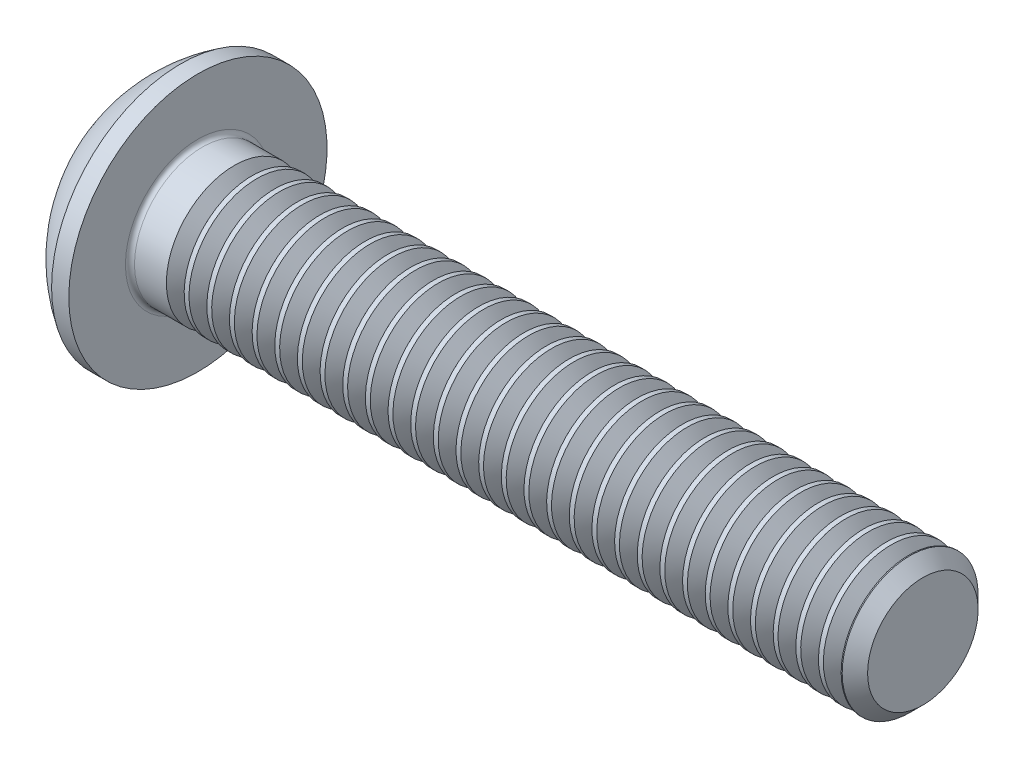
SolidWorks part; units mm, degrees
ref_plane "Plane1" through (0, 0, 0) normal (0, 0, 1) x (1, 0, 0)
ref_plane "Plane2" through (0, 0, 0) normal (0, 1, 0) x (1, 0, 0)
ref_plane "Plane3" through (0, 0, 0) normal (1, 0, 0) x (0, 0, -1)
sketch "BodySke" plane through (0, 0, 0) normal (0, 0, 1) x (1, 0, 0)
  line L0 (17.65, 0) -> (17.65, 1.2195)
  line L1 (17.3695, 1.5) -> (1.65, 1.5)
  line L2 (1.65, 1.5) -> (1.65, 2.85)
  line L3 (1.65, 2.85) -> (1.27, 2.85)
  line L4 (0, 0) -> (101.6, 0) construction
  line L5 (1.65, -2.85) -> (1.27, -2.85) construction
  line L6 (55.6768, -1.5) -> (1.65, -1.5) construction
  line L7 (17.65, 0) -> (0, 0)
  line L8 (0, 1.425) -> (0, -1.425) construction
  line L9 (0, 0) -> (0, 1.425)
  line L10 (17.65, 1.2195) -> (17.3695, 1.5)
  line L11 (17.65, -1.2195) -> (17.3695, -1.5) construction
  line L12 (2.15, 9.525) -> (2.15, -1.5) construction
  line L13 (1.65, 9.525) -> (1.65, -1.5) construction
  arc A1 (0, 1.425) -> (1.27, 2.85) centre (3.0334, 0) cw
  dimension "Diameter" = 3
  dimension "Length" = 16
  dimension "Head_dia" = 5.7
  dimension "D1" = 2.85
  dimension "Head_ht" = 1.65
  dimension "Head_side_ht" = 0.38
  dimension "Minor_dia" = 2.439
  dimension "Body_ch_ang" = 45
  dimension "Advance" = 0.5
  dimension "Thread_nom" = 16
revolve "BaseBody" add sketch "BodySke" angle 360 about L4
cosmetic thread "ThreadCosmetic" [suppressed] parameters "Thread_length"=15, "Thread_minor"=2.439
fillet "Fillet1" radius 0.1 1 edges at (1.65, 0, 1.5)
sketch "Sketch2" plane through (0, 0, 0) normal (0, 0, 1) x (1, 0, 0)
  line L0 (0, 1) -> (1.04, 1)
  line L1 (1.04, 1) -> (1.6174, 0)
  line L3 (1.6174, 0) -> (0, 0)
  line L4 (0, 0) -> (0, 1)
  line L5 (0, -1) -> (1.04, -1) construction
  line L6 (0, 0) -> (47.625, 0) construction
  dimension "D2" = 60
  dimension "PreBroach_depth" = 1.04
  dimension "PreBroach_dia" = 2
revolve "PreBroach" cut sketch "Sketch2" angle 360 about L6
sketch "Sketch3" plane through (0, 0, 0) normal (1, 0, 0) x (0, 0, -1)
  line L0 (-1, -0.5774) -> (-1, 0.5774)
  line L1 (-1, 0.5774) -> (0, 1.1547)
  line L2 (0, 1.1547) -> (1, 0.5774)
  line L3 (1, 0.5774) -> (1, -0.5774)
  line L4 (1, -0.5774) -> (0, -1.1547)
  line L5 (0, -1.1547) -> (-1, -0.5774)
  dimension "Hex_size" = 2
  dimension "D3" = 2
  dimension "D1" = 1
  dimension "D2" = 1
extrude "Hex" cut sketch "Sketch3" along normal blind 1.04
sketch "ThdSchSke" plane through (0, 0, 0) normal (0, 0, 1) x (1, 0, 0)
  line L0 (2.65, -1.2195) -> (2.4536, -1.5)
  line L1 (2.65, -1.2195) -> (2.8464, -1.5)
  line L2 (2.8464, -1.5) -> (2.8464, -1.875)
  line L3 (-3.175, 0) -> (5.1513, 0) construction
  line L5 (2.8464, -1.875) -> (2.4536, -1.875)
  line L6 (2.4536, -1.875) -> (2.4536, -1.5)
  dimension "Diameter" = 3
  dimension "Thread_minor" = 2.439
  dimension "SideAngle" = 55
  dimension "VeeAngle" = 70
  dimension "Overcut" = 3.75
  dimension "Start" = 2.65
revolve "ThreadSchematic" cut sketch "ThdSchSke" angle 360 about L3
pattern_linear "ThdSchPat" count 30 spacing 0.5 along (1, 0, 0) of "ThreadSchematic"
equation "\"D1@BodySke\" = \"Head_dia@BodySke\" * .5"
equation "\"Thread_minor@ThreadCosmetic\" = \"Minor_dia@BodySke\""
equation "\"D1@Sketch3\" = \"Hex_size@Sketch3\" / 2"
equation "\"D2@Sketch3\" = \"D1@Sketch3\""
equation "\"D3@Sketch3\" = \"Hex_size@Sketch3\""
equation "\"Thread_length@ThreadCosmetic\" = ((sgn( (\"Length@BodySke\" - \"Advance@BodySke\" * 2.0) - \"Thread_nom@BodySke\" )-1)*( (\"Length@BodySke\" - \"Advance@BodySke\" * 2.0) - \"Thread_nom@BodySke\" ))/-2+ \"Thread_nom@BodySke\""
equation "\"Thread_minor@ThdSchSke\" = \"Minor_dia@BodySke\""
equation "\"Diameter@ThdSchSke\" = \"Diameter@BodySke\""
equation "\"Overcut@ThdSchSke\" = \"Diameter@BodySke\" * 1.25"
equation "\"Start@ThdSchSke\" = \"Head_ht@BodySke\" + \"Length@BodySke\" - \"Thread_length@ThreadCosmetic\"  '---Non-countersunk---"
equation "\"Num_threads@ThdSchPat\" = int( \"Thread_length@ThreadCosmetic\" / \"Advance@BodySke\" + 0.999 )  + 1"
equation "\"Advance@ThdSchPat\" = \"Thread_length@ThreadCosmetic\" /  (\"Num_threads@ThdSchPat\" - 1) 'relax it"
equation "\"Num_threads@ThdSchPat\" = \"Num_threads@ThdSchPat\" - sgn( \"Num_threads@ThdSchPat\" - 1) '---chamfered tips only---"
